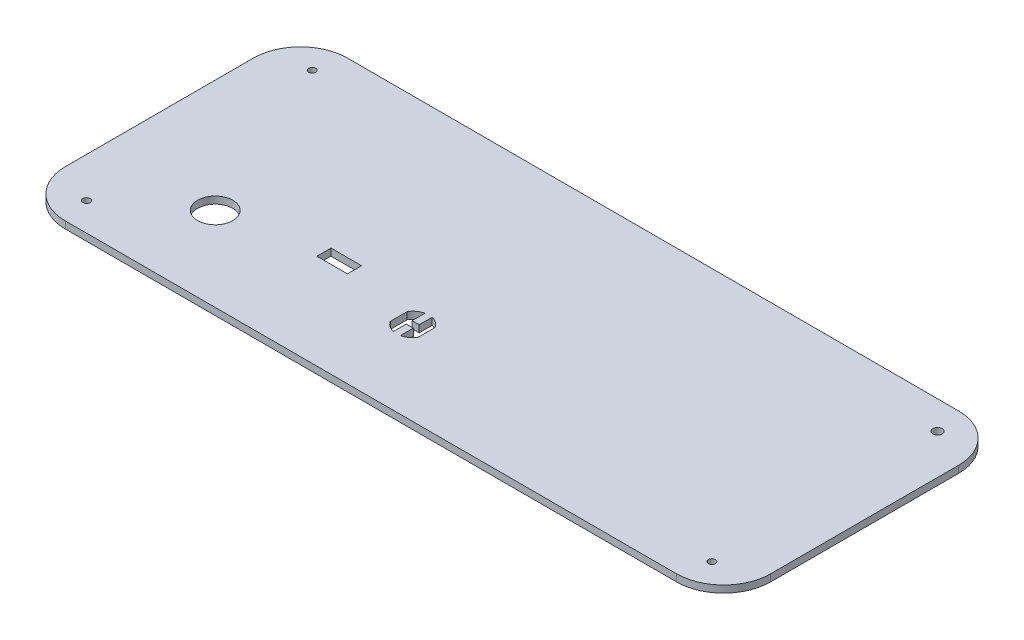
SolidWorks part; units mm, degrees
ref_plane "Спереди" through (0, 0, 0) normal (0, 0, 1) x (1, 0, 0)
ref_plane "Сверху" through (0, 0, 0) normal (0, 1, 0) x (1, 0, 0)
ref_plane "Справа" through (0, 0, 0) normal (1, 0, 0) x (0, 0, -1)
sketch "Эскиз2" plane through (0, 0, 0) normal (0, 1, 0) x (1, 0, 0)
  line L0 (-300, 0) -> (0, 120) construction
  line L1 (0, 0) -> (-300, 0)
  line L2 (0, 0) -> (0, 120)
  line L3 (0, 120) -> (-300, 120)
  line L4 (-300, 0) -> (-300, 120)
  line L6 (-300, 120) -> (0, 0) construction
  line L7 (-300, 28) -> (0, 92) construction
  line L11 (0, 60) -> (-300, 60) construction
  line L12 (-150, 120) -> (-150, 0) construction
  line L13 (-200.5, 46.4965) -> (-200.5, 40.4965)
  line L14 (-213.5, 46.4965) -> (-200.5, 46.4965)
  line L18 (-173.9, 39.3242) -> (-173.9, 32.1688)
  line L19 (-162.1, 39.3242) -> (-162.1, 32.1688)
  line L21 (-213.5, 46.4965) -> (-213.5, 40.4965)
  line L22 (-213.5, 40.4965) -> (-200.5, 40.4965)
  line L23 (-166.5, 42.4815) -> (-166.5, 36.9965)
  line L24 (-169.5, 42.4815) -> (-169.5, 36.9965)
  line L25 (-169.5, 36.9965) -> (-166.5, 36.9965)
  line L26 (-169.5, 34.4965) -> (-166.5, 34.4965)
  line L27 (-169.5, 34.4965) -> (-169.5, 29.0115)
  line L28 (-166.5, 34.4965) -> (-166.5, 29.0115)
  circle A0 centre (-283, 108) radius 1.5
  circle A1 centre (-17, 108) radius 2
  circle A2 centre (-17, 12) radius 1.5
  circle A3 centre (-283, 12) radius 1.5
  arc A12 (-173.9, 32.1688) -> (-169.5, 29.0115) centre (-168, 35.7465) ccw
  circle A14 centre (-252, 35.7465) radius 7.5
  arc A15 (-162.1, 39.3242) -> (-166.5, 42.4815) centre (-168, 35.7465) ccw
  arc A16 (-169.5, 42.4815) -> (-173.9, 39.3242) centre (-168, 35.7465) ccw
  arc A17 (-166.5, 29.0115) -> (-162.1, 32.1688) centre (-168, 35.7465) ccw
  point P18 (-150, 60)
  point P20 (-300, 28)
  point P21 (0, 92)
  point P28 (-174.9, 35.7465)
  point P29 (-161.1, 35.7465)
  point P40 (-173.9, 35.7465)
  point P43 (-162.1, 35.7465)
  point P49 (-173.9, 36.9965)
  point P50 (-173.9, 34.4965)
  point P51 (-162.1, 36.9965)
  point P52 (-162.1, 34.4965)
  dimension "D5" = 3
  dimension "D6" = 4
  dimension "D7" = 3
  dimension "D8" = 3
  dimension "D18" = 84
  dimension "D15" = 5.485
  dimension "D21" = 48
  dimension "D22" = 35.7465
  dimension "D23" = 13.8
  dimension "D24" = 6
  dimension "D27" = 40.4965
  dimension "D30" = 1
  dimension "D25" = 15
  dimension "D1" = 300
  dimension "D2" = 120
  dimension "D3" = 266
  dimension "D4" = 96
  dimension "D9" = 266
  dimension "D10" = 12
  dimension "D11" = 17
  dimension "D12" = 96
  dimension "D13" = 17
  dimension "D14" = 12
  dimension "D19" = 28
  dimension "D20" = 28
  dimension "D26" = 13
  dimension "D28" = 86.5
  dimension "D29" = 1
  dimension "D31" = 1.5
  dimension "D32" = 1.5
  dimension "D33" = 1.25
  dimension "D34" = 1.25
  dimension "D35" = 1.25
  dimension "D36" = 1.25
  dimension "D37" = 5.485
  dimension "D38" = 5.485
extrude "Бобышка-Вытянуть1" add sketch "Эскиз2" along normal blind 3
fillet "Скругление1" radius 20 4 edges at (-300, 1.5, -120) (0, 1.5, -120) (0, 1.5, 0) (-300, 1.5, 0)
